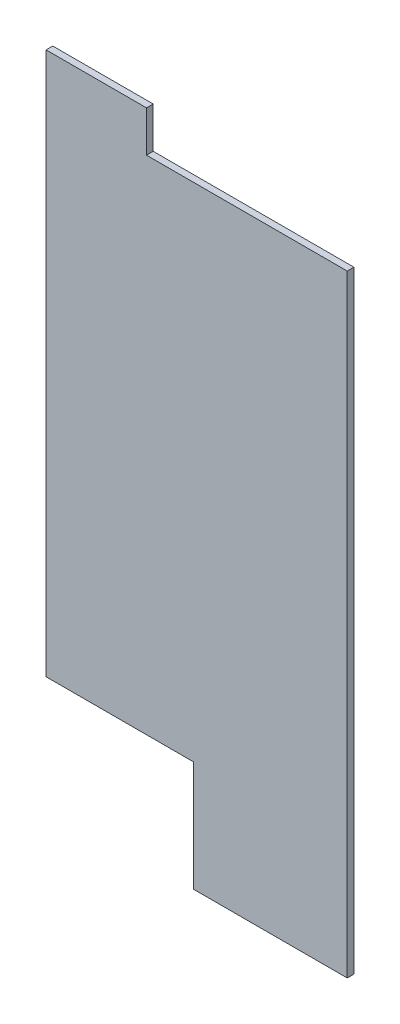
SolidWorks part; units mm, degrees
ref_plane "Front Plane" through (0, 0, 0) normal (0, 0, 1) x (1, 0, 0)
ref_plane "Top Plane" through (0, 0, 0) normal (0, 1, 0) x (1, 0, 0)
ref_plane "Right Plane" through (0, 0, 0) normal (1, 0, 0) x (0, 0, -1)
sketch "Sketch1" plane through (0, 0, 0) normal (0, 0, 1) x (1, 0, 0)
  line L1 (22.5, -37.5) -> (-22.5, -37.5)
  line L2 (22.5, -37.5) -> (22.5, 37.5)
  line L3 (22.5, 37.5) -> (-22.5, 37.5)
  line L4 (-22.5, -37.5) -> (-22.5, 37.5)
  line L5 (22.5, -37.5) -> (-22.5, 37.5) construction
  line L6 (22.5, 37.5) -> (-22.5, -37.5) construction
  point P0 (0, 0)
  dimension "D1" = 45
  dimension "D2" = 75
extrude "Boss-Extrude1" add sketch "Sketch1" along normal blind 1
sketch "Sketch2" plane through (0, 0, 1) normal (0, 0, 1) x (1, 0, 0)
  line L0 (-22.5, -37.5) -> (22.5, -37.5) construction
  line L1 (-0.5, -37.5) -> (22.5, -37.5)
  line L2 (-0.5, -37.5) -> (-0.5, -53.9793)
  line L3 (-0.5, -53.9793) -> (22.5, -53.9793)
  line L4 (22.5, -37.5) -> (22.5, -53.9793)
  line L5 (22.5, -37.5) -> (22.5, 37.5) construction
  point P8 (22.5, -53.9793)
  dimension "D1" = 23
extrude "Boss-Extrude2" add sketch "Sketch2" against normal blind 1
sketch "Sketch3" plane through (0, 0, 1) normal (0, 0, 1) x (1, 0, 0)
  line L0 (22.5, 37.5) -> (-22.5, 37.5) construction
  line L1 (-22.5, 43.622) -> (-7.494, 43.622)
  line L2 (-22.5, 43.622) -> (-22.5, 37.5)
  line L3 (-22.5, 37.5) -> (-7.494, 37.5)
  line L4 (-7.494, 43.622) -> (-7.494, 37.5)
  line L5 (-22.5, 37.5) -> (-22.5, -37.5) construction
  point P14 (11.5775, 46.0709)
  point P15 (-6.8755, 46.0709)
  point P16 (-22.5, 43.6654)
  point P17 (-7.9643, 43.5263)
  point P18 (5.8562, 43.5887)
  point P19 (0, 0)
  point P20 (4.4803, 43.5763)
  point P21 (5.1875, 43.622)
  point P22 (0, 0)
  point P23 (-7.494, 37.5)
  point P24 (0, 0)
  point P25 (4.1822, 37.5)
extrude "Boss-Extrude3" add sketch "Sketch3" against normal blind 1
